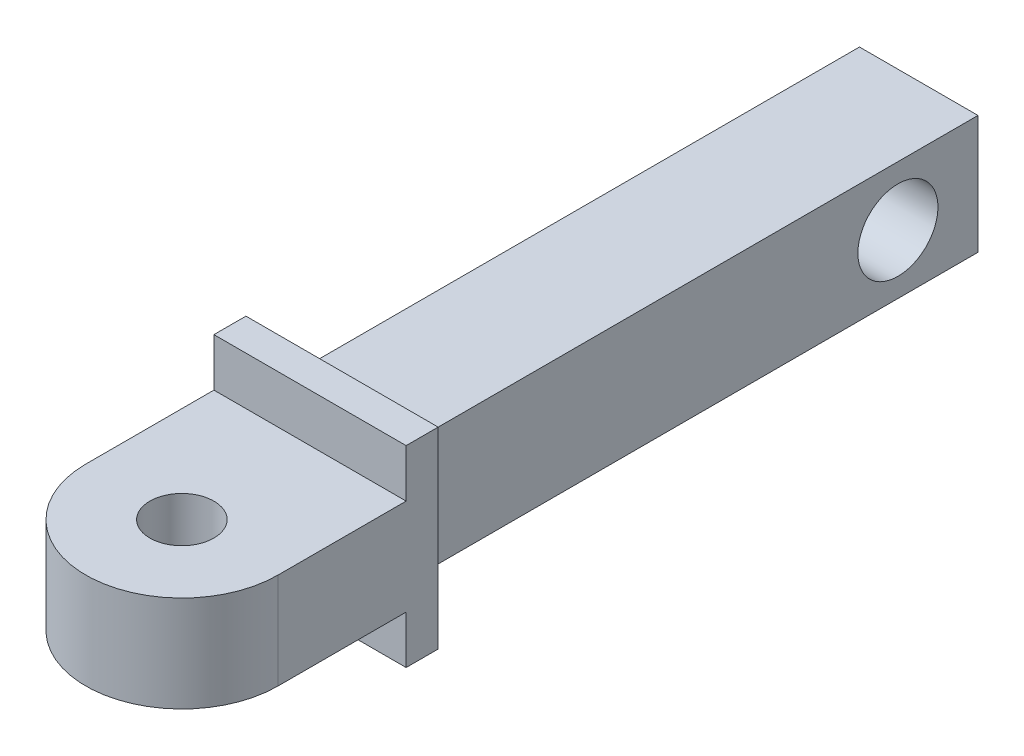
SolidWorks part; units mm, degrees
ref_plane "정면" through (0, 0, 0) normal (0, 0, 1) x (1, 0, 0)
ref_plane "윗면" through (0, 0, 0) normal (0, 1, 0) x (1, 0, 0)
ref_plane "우측면" through (0, 0, 0) normal (1, 0, 0) x (0, 0, -1)
sketch "스케치1" plane through (0, 0, 0) normal (0, 0, 1) x (1, 0, 0)
  line L1 (3, 3) -> (-3, 3)
  line L2 (3, 3) -> (3, -3)
  line L3 (3, -3) -> (-3, -3)
  line L4 (-3, 3) -> (-3, -3)
  point P4 (3, 0)
  point P5 (0, 3)
  dimension "D1" = 6
  dimension "D2" = 6
extrude "보스-돌출1" add sketch "스케치1" along normal blind 1
sketch "스케치2" plane through (0, 0, 0) normal (0, 1, 0) x (1, 0, 0)
  line L0 (3, -1) -> (3, 0) construction
  line L1 (-3, -1) -> (3, -1)
  line L2 (-3, -1) -> (-3, -5)
  line L4 (3, -1) -> (3, -5)
  arc A0 (-3, -5) -> (3, -5) centre (0, -5) ccw
  circle A1 centre (0, -5) radius 1
  point P6 (0, -4.9383)
  point P9 (-0.1246, -5)
  dimension "D2" = 2
  dimension "D1" = 4
extrude "보스-돌출2" add sketch "스케치2" along normal blind 1.5 and the other way blind 1.5
sketch "스케치3" plane through (0, 0, 0) normal (0, 0, -1) x (-1, 0, 0)
  line L1 (1.85, 1.85) -> (-1.85, 1.85)
  line L2 (1.85, 1.85) -> (1.85, -1.85)
  line L3 (1.85, -1.85) -> (-1.85, -1.85)
  line L4 (-1.85, 1.85) -> (-1.85, -1.85)
  point P4 (0, 1.85)
  point P6 (1.85, 0)
  dimension "D1" = 3.7
extrude "보스-돌출3" add sketch "스케치3" along normal blind 18
sketch "스케치4" plane through (-1.85, 0, 0) normal (-1, 0, 0) x (0, 0, 1)
  line L0 (-18, -1.85) -> (-18, 1.85) construction
  circle A0 centre (-15.5, 0) radius 1.25
  point P5 (-18, 0)
  dimension "D1" = 2.5
  dimension "D2" = 2.5
extrude "컷-돌출1" cut sketch "스케치4" against normal up to surface (3.7 mm away) up to face at (1.85, 0, -9)
